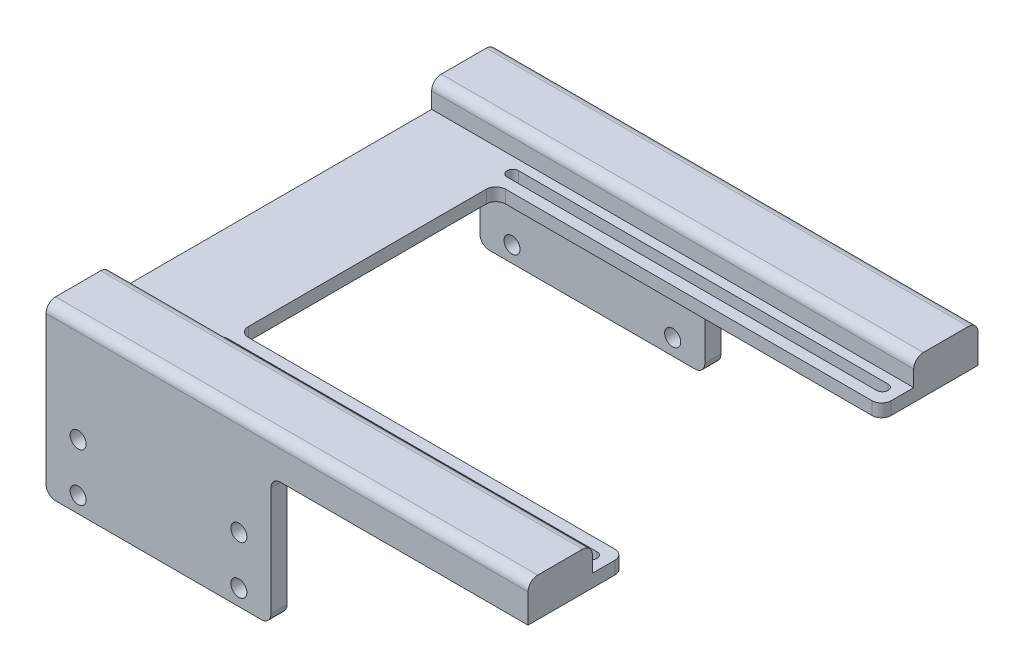
SolidWorks part; units mm, degrees
ref_plane "Front Plane" through (0, 0, 0) normal (0, 0, 1) x (1, 0, 0)
ref_plane "Top Plane" through (0, 0, 0) normal (0, 1, 0) x (1, 0, 0)
ref_plane "Right Plane" through (0, 0, 0) normal (1, 0, 0) x (0, 0, -1)
sketch "Sketch1" plane through (0, 0, 0) normal (0, 1, 0) x (1, 0, 0)
  line L1 (-75, 70) -> (75, 70)
  line L2 (-75, 70) -> (-75, -70)
  line L3 (-75, -70) -> (75, -70)
  line L4 (75, 70) -> (75, -70)
  line L5 (-75, 70) -> (75, -70) construction
  line L6 (-75, -70) -> (75, 70) construction
  point P0 (0, 0)
  dimension "D1" = 150
  dimension "D2" = 140
extrude "Boss-Extrude1" add sketch "Sketch1" along normal blind 12
sketch "Sketch4" plane through (0, 0, 0) normal (0, -1, 0) x (1, 0, 0)
  line L0 (-75, -70) -> (-5, -70)
  line L1 (-75, -70) -> (-75, 70)
  line L2 (-5, -70) -> (-5, 70)
  line L3 (-75, 70) -> (-5, 70)
  line L4 (75, -70) -> (-75, -70) construction
  line L5 (75, 70) -> (75, -70) construction
  line L6 (-75, -70) -> (-75, 70) construction
  line L7 (-75, 70) -> (75, 70) construction
  dimension "D1" = 80
extrude "Boss-Extrude2" add sketch "Sketch4" along normal blind 40
sketch "Sketch5" plane through (0, 0, 70) normal (0, 0, 1) x (1, 0, 0)
  line L1 (-5, -40) -> (-75, -40) construction
  line L2 (-75, 12) -> (-75, -40) construction
  circle A0 centre (-65, -35) radius 2.5
  circle A1 centre (-15, -35) radius 2.5
  circle A2 centre (-15, -20) radius 2.5
  circle A3 centre (-65, -20) radius 2.5
  dimension "D1" = 5
  dimension "D2" = 5
  dimension "D3" = 10
  dimension "D4" = 2
  dimension "D5" = 2
extrude "Cut-Extrude1" cut sketch "Sketch5" against normal through all
sketch "Sketch7" plane through (0, 12, 0) normal (0, 1, 0) x (1, 0, 0)
  line L0 (-75, 50) -> (-75, -50)
  line L1 (-75, 50) -> (75, 50)
  line L2 (-75, -50) -> (75, -50)
  line L3 (75, 50) -> (75, -50)
  line L4 (-75, 70) -> (-75, -70) construction
  line L5 (75, 70) -> (-75, 70) construction
  line L8 (75, -70) -> (75, 70) construction
  dimension "D1" = 100
  dimension "D2" = 20
extrude "Cut-Extrude2" cut sketch "Sketch7" against normal blind 8
sketch "Sketch8" plane through (0, 0, 0) normal (0, -1, 0) x (1, 0, 0)
  line L0 (75, 40) -> (75, -40)
  line L1 (75, 40) -> (-45, 40)
  line L2 (75, -40) -> (-45, -40)
  line L3 (-45, 40) -> (-45, -40)
  line L4 (75, 70) -> (75, -70) construction
  line L5 (-5, 70) -> (75, 70) construction
  dimension "D1" = 80
  dimension "D2" = 30
  dimension "D3" = 120
extrude "Cut-Extrude3" cut sketch "Sketch8" against normal through all both and the other way through all
sketch "Sketch9" plane through (0, 4, 0) normal (0, 1, 0) x (1, 0, 0)
  line L0 (-45, 45.25) -> (70, 45.25) construction
  line L1 (-45, 47) -> (70, 47)
  line L2 (-45, 43.5) -> (70, 43.5)
  line L3 (75, 40) -> (75, 50) construction
  line L5 (0, 0) -> (117.9162, 0) construction
  line L6 (-45, -45.25) -> (70, -45.25) construction
  line L7 (-45, -47) -> (70, -47)
  line L8 (-45, -43.5) -> (70, -43.5)
  line L9 (75, 50) -> (-75, 50) construction
  line L10 (-45, -40) -> (-45, 40) construction
  arc A0 (-45, 47) -> (-45, 43.5) centre (-45, 45.25) ccw
  arc A1 (70, 43.5) -> (70, 47) centre (70, 45.25) ccw
  arc A2 (-45, -47) -> (-45, -43.5) centre (-45, -45.25) cw
  arc A3 (70, -43.5) -> (70, -47) centre (70, -45.25) cw
  point P2 (12.5, 45.25)
  point P16 (12.5, -45.25)
  dimension "D2" = 5
  dimension "D3" = 0
  dimension "D1" = 3.5
  dimension "D4" = 3
extrude "Cut-Extrude4" cut sketch "Sketch9" against normal through all
sketch "Sketch11" plane through (-5, 0, 0) normal (1, 0, 0) x (0, 0, -1)
  line L0 (-65, -40) -> (-65, 0)
  line L1 (-65, -40) -> (65, -40)
  line L2 (-65, 0) -> (65, 0)
  line L3 (65, -40) -> (65, 0)
  line L4 (-40, -40) -> (-43.5, -40) construction
  line L5 (-70, -40) -> (-70, 0) construction
  line L6 (70, -40) -> (70, 0) construction
  line L7 (-40, 0) -> (-43.5, 0) construction
  dimension "D1" = 5
  dimension "D2" = 5
  dimension "D3" = 0
extrude "Cut-Extrude6" cut sketch "Sketch11" against normal through all
fillet "Fillet5" radius 3 2 edges at (-40, 0, 65) (-40, 0, -65)
fillet "Fillet6" radius 3 2 edges at (-5, 0, -66) (-5, 0, 66)
fillet "Fillet7" radius 3 2 edges at (0, 12, 70) (0, 12, -70)
fillet "Fillet8" radius 3 2 edges at (0, 12, -50) (0, 12, 50)
fillet "Fillet9" radius 3 4 edges at (-5, -40, -67.5) (-5, -40, 67.5) (-75, -40, 67.5) (-75, -40, -67.5)
fillet "Fillet10" radius 3 2 edges at (-45, 2, 40) (-45, 2, -40)
fillet "Fillet11" radius 3 2 edges at (75, 2, 40) (75, 2, -40)
